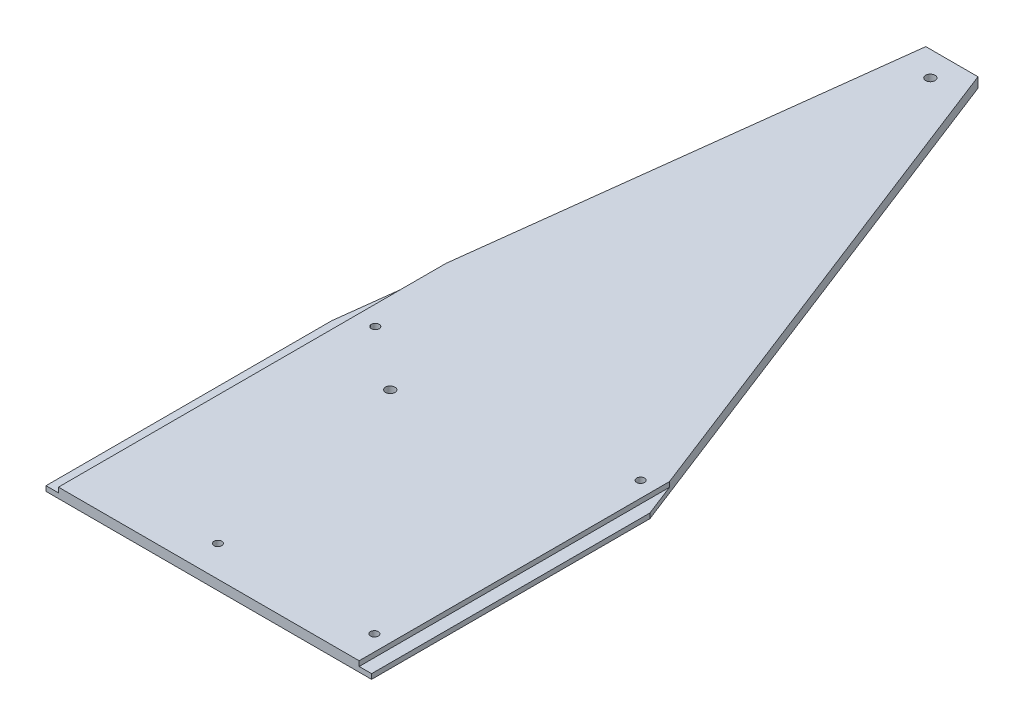
SolidWorks part; units mm, degrees
ref_plane "Front Plane" through (0, 0, 0) normal (0, 0, 1) x (1, 0, 0)
ref_plane "Top Plane" through (0, 0, 0) normal (0, 1, 0) x (1, 0, 0)
ref_plane "Right Plane" through (0, 0, 0) normal (1, 0, 0) x (0, 0, -1)
sketch "Sketch2" plane through (0, 0, 0) normal (0, 1, 0) x (1, 0, 0)
  line L0 (0, 0) -> (0, 182.5625)
  line L1 (0, 182.5625) -> (41.275, 520.7)
  line L2 (41.275, 520.7) -> (74.6125, 520.7)
  line L3 (74.6125, 520.7) -> (207.9625, 177.8)
  line L4 (207.9625, 177.8) -> (207.9625, 0)
  line L5 (207.9625, 0) -> (0, 0)
  line L6 (39.3372, 504.825) -> (80.7861, 504.825) construction
  line L7 (60.0617, 159.795) -> (0, 159.795) construction
  line L8 (60.0617, 504.825) -> (60.0617, 0) construction
  circle A0 centre (60.0617, 504.825) radius 3
  circle A1 centre (20.3017, 190.035) radius 2.5
  circle A2 centre (190.0817, 189.735) radius 2.5
  circle A3 centre (190.0017, 19.755) radius 2.5
  circle A4 centre (90.0317, 19.755) radius 2.5
  circle A5 centre (60.0617, 159.795) radius 3
  point P19 (0, 0)
  point P20 (60.0617, 504.825)
  point P22 (20.6375, 184.2707)
  point P25 (150.541, 184.2707)
  point P26 (0, 0)
  dimension "D7" = 6
  dimension "D14" = 5
  dimension "D1" = 207.9625
  dimension "D2" = 182.5625
  dimension "D3" = 177.8
  dimension "D4" = 133.35
  dimension "D5" = 33.3375
  dimension "D6" = 520.7
  dimension "D8" = 15.875
  dimension "D9" = 345.03
  dimension "D10" = 39.76
  dimension "D11" = 130.02
  dimension "D12" = 314.79
  dimension "D13" = 315.09
  dimension "D15" = 29.97
  dimension "D16" = 129.94
  dimension "D17" = 485.07
extrude "Boss-Extrude1" add sketch "Sketch2" along normal blind 6.35
sketch "Sketch3" plane through (0, 0, 0) normal (0, 0, 1) x (1, 0, 0)
  line L2 (0, 3.175) -> (7.9375, 3.175)
  line L3 (7.9375, 3.175) -> (7.9375, 6.35)
  line L4 (0, 6.35) -> (207.9625, 6.35) construction
  line L6 (200.025, 6.35) -> (200.025, 3.175)
  line L7 (200.025, 3.175) -> (207.9625, 3.175)
  line L11 (7.9375, 6.35) -> (0, 6.35)
  line L12 (0, 6.35) -> (0, 3.175)
  line L13 (200.025, 6.35) -> (207.9625, 6.35)
  line L14 (207.9625, 6.35) -> (207.9625, 3.175)
  dimension "D1" = 7.9375
  dimension "D2" = 7.9375
  dimension "D3" = 3.175
  dimension "D4" = 3.175
extrude "Cut-Extrude1" cut sketch "Sketch3" against normal through all both and the other way through all
